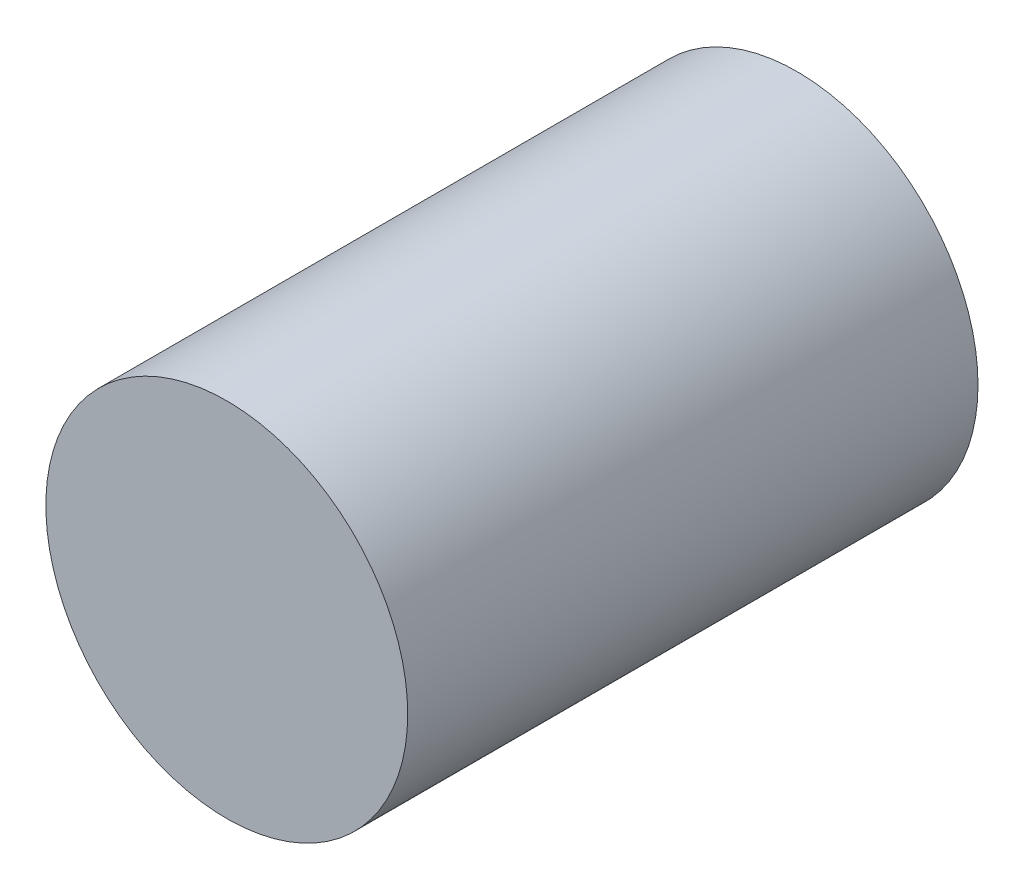
SolidWorks part; units mm, degrees
ref_plane "Спереди" through (0, 0, 0) normal (0, 0, 1) x (1, 0, 0)
ref_plane "Сверху" through (0, 0, 0) normal (0, 1, 0) x (1, 0, 0)
ref_plane "Справа" through (0, 0, 0) normal (1, 0, 0) x (0, 0, -1)
sketch "Эскиз1" plane through (0, 0, 0) normal (0, 0, 1) x (1, 0, 0)
  circle A0 centre (0, 62) radius 7.9 construction
  circle A1 centre (0, 62) radius 7.9
extrude "Бобышка-Вытянуть1" add sketch "Эскиз1" against normal up to surface (24.9 mm away)
